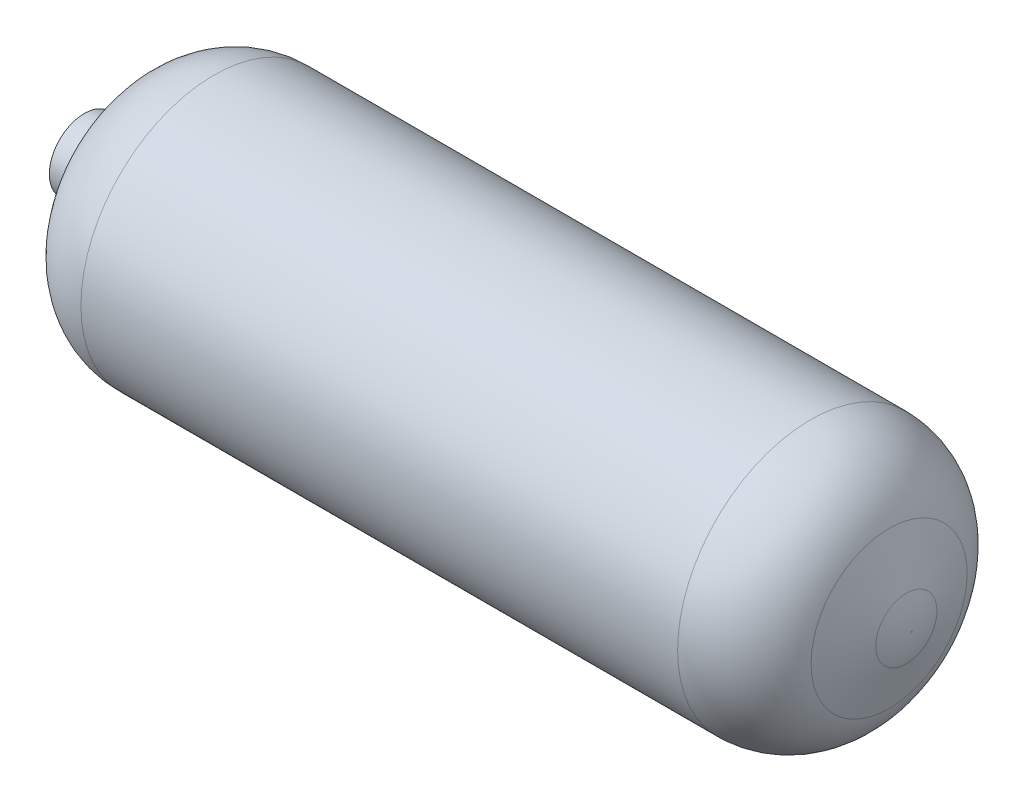
SolidWorks part; units mm, degrees
material "6061-T6 (SS)"
ref_plane "Front Plane" through (0, 0, 0) normal (0, 0, 1) x (1, 0, 0)
ref_plane "Top Plane" through (0, 0, 0) normal (0, 1, 0) x (1, 0, 0)
ref_plane "Right Plane" through (0, 0, 0) normal (1, 0, 0) x (0, 0, -1)
sketch "Sketch1" plane through (0, 0, 0) normal (0, 0, 1) x (1, 0, 0)
  line L0 (-0.2756, 0.129) -> (0.3032, 0.129)
  line L1 (-0.4012, 0.034) -> (-0.4012, 0)
  line L2 (-0.4012, 0.034) -> (-0.3773, 0.034)
  line L4 (-0.3729, 0.0367) -> (-0.3487, 0.0842)
  line L5 (-0.4012, 0) -> (0.4012, 0) construction
  line L6 (0.3794, 0.0757) -> (0.3961, 0.0297)
  line L7 (-0.4012, 0) -> (0.4012, 0)
  line L8 (0.4012, 0) -> (0.4012, 0.0006)
  arc A0 (-0.2756, 0.129) -> (-0.3487, 0.0842) centre (-0.2756, 0.047) ccw
  arc A1 (0.3032, 0.129) -> (0.3794, 0.0757) centre (0.3032, 0.048) cw
  arc A2 (0.4012, 0.0006) -> (0.3961, 0.0297) centre (0.3163, 0.0006) ccw
  arc A3 (-0.3729, 0.0367) -> (-0.3773, 0.034) centre (-0.3773, 0.039) cw
  point P6 (-0.3742, 0.034)
  dimension "D8" = 0.082
  dimension "D11" = 0.081
  dimension "D13" = 0.085
  dimension "D6" = 0.005
  dimension "D2" = 0.2756
  dimension "D3" = 0.034
  dimension "D4" = 0.3032
  dimension "D5" = 0.027
  dimension "D7" = 117
  dimension "D9" = 0.8025
  dimension "D10" = 110
revolve "Revolve2" add sketch "Sketch1" angle 360 about L7
scale "Scale1" scale about origin uniform scaling yes scale factor 649.767462
shell "Shell2" thickness 5.588
sketch "Sketch2" plane through (0, 0, 0) normal (0, 1, 0) x (1, 0, 0)
  line L7 (246.4991, 49.1898) -> (257.3884, 19.2716)
  line L8 (260.7192, 0.3818) -> (197.042, 0.3818)
  line L9 (197.042, -83.82) -> (197.042, 83.82) construction
  line L10 (197.042, 0.3818) -> (197.042, 83.82)
  line L11 (-226.5465, 54.7281) -> (-242.2713, 23.8664)
  line L12 (-260.7192, 22.0921) -> (-245.1667, 22.0921)
  line L13 (-260.7192, 22.0921) -> (-260.7192, 0)
  line L14 (-260.7192, 22.0921) -> (-260.7192, -22.0921) construction
  line L15 (-260.7192, 0) -> (-179.0728, 0)
  line L16 (-179.0728, -83.82) -> (-179.0728, 83.82) construction
  line L17 (-179.0728, 0) -> (-179.0728, 83.82)
  arc A2 (197.042, 83.82) -> (246.4991, 49.1898) centre (197.042, 31.1888) cw
  arc A3 (257.3884, 19.2716) -> (260.7192, 0.3818) centre (205.489, 0.3818) cw
  arc A4 (-179.0728, 83.82) -> (-226.5465, 54.7281) centre (-179.0728, 30.5391) ccw
  arc A5 (-242.2713, 23.8664) -> (-245.1667, 22.0921) centre (-245.1667, 25.3417) cw
revolve "Added to make cavity cut for shoulder" [suppressed] add sketch "Sketch2" angle 360 about L15
sketch "Sketch3" plane through (-260.7192, 0, 0) normal (-1, 0, 0) x (0, 0, 1)
  circle A0 centre (0, 0) radius 111.5906
  circle A1 centre (0, 0) radius 46.355
  dimension "D1" = 92.71
